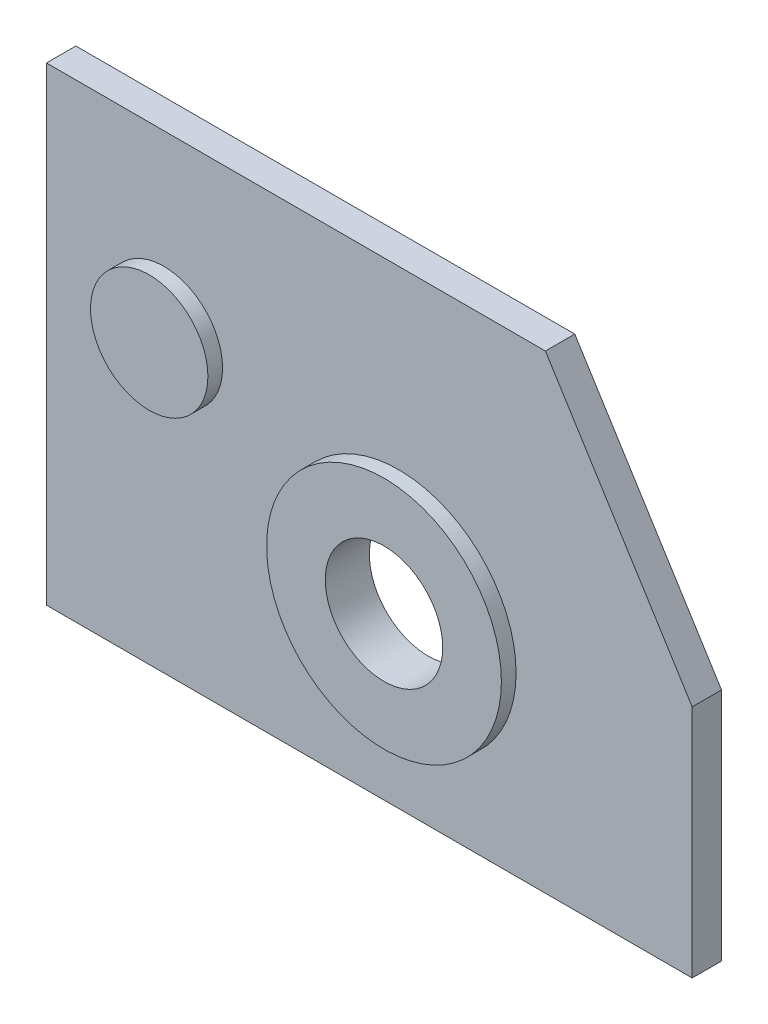
SolidWorks part; units mm, degrees
ref_plane "Front Plane" through (0, 0, 0) normal (0, 0, 1) x (1, 0, 0)
ref_plane "Top Plane" through (0, 0, 0) normal (0, 1, 0) x (1, 0, 0)
ref_plane "Right Plane" through (0, 0, 0) normal (1, 0, 0) x (0, 0, -1)
sketch "Sketch1" plane through (0, 0, 0) normal (0, 0, 1) x (1, 0, 0)
  line L0 (0, 0) -> (139.7, 0)
  line L1 (139.7, 0) -> (139.7, 50.8)
  line L2 (139.7, 50.8) -> (107.95, 101.6)
  line L3 (107.95, 101.6) -> (0, 101.6)
  line L4 (0, 101.6) -> (0, 0)
  dimension "D1" = 101.6
  dimension "D2" = 139.7
  dimension "D3" = 107.95
  dimension "D4" = 50.8
extrude "Boss-Extrude2" add sketch "Sketch1" along normal blind 6.35
sketch "Sketch2" plane through (0, 0, 6.35) normal (0, 0, 1) x (1, 0, 0)
  circle A3 centre (25.4, 63.5) radius 12.7
  circle A4 centre (76.2, 38.1) radius 12.7
  circle A5 centre (76.2, 38.1) radius 25.4
  dimension "D5" = 38.1
  dimension "D6" = 63.5
  dimension "D7" = 25.4
  dimension "D1" = 25.4
  dimension "D2" = 25.4
  dimension "D3" = 50.8
  dimension "D4" = 76.2
extrude "Boss-Extrude4" add sketch "Sketch2" along normal blind 3.175
sketch "Sketch5" plane through (0, 0, 6.35) normal (0, 0, 1) x (1, 0, 0)
  circle A0 centre (76.2, 38.1) radius 12.7
  dimension "D3" = 25.4
  dimension "D1" = 38.1
  dimension "D2" = 76.2
extrude "Cut-Extrude1" cut sketch "Sketch5" against normal blind 127
